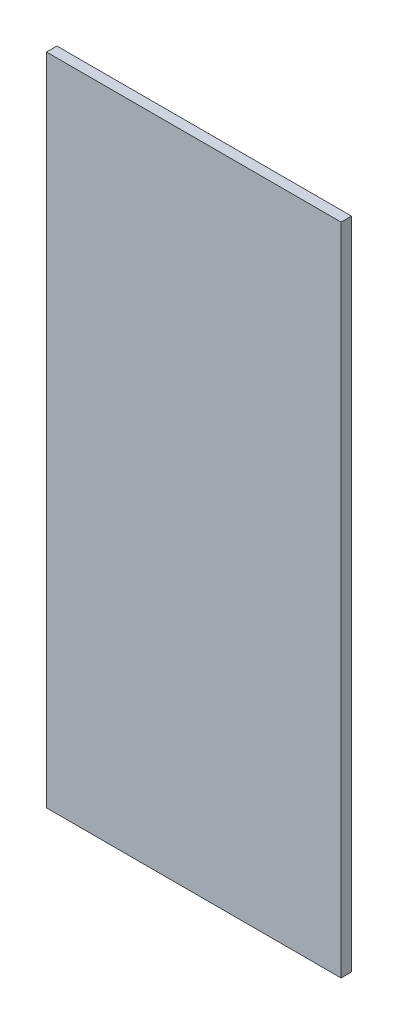
SolidWorks part; units mm, degrees
ref_plane "Front Plane" through (0, 0, 0) normal (0, 0, 1) x (1, 0, 0)
ref_plane "Top Plane" through (0, 0, 0) normal (0, 1, 0) x (1, 0, 0)
ref_plane "Right Plane" through (0, 0, 0) normal (1, 0, 0) x (0, 0, -1)
sketch "Sketch1" plane through (0, 0, 0) normal (0, 0, 1) x (1, 0, 0)
  line L1 (45, -100) -> (-45, -100)
  line L2 (45, -100) -> (45, 100)
  line L3 (45, 100) -> (-45, 100)
  line L4 (-45, -100) -> (-45, 100)
  line L5 (45, -100) -> (-45, 100) construction
  line L6 (45, 100) -> (-45, -100) construction
  point P0 (0, 0)
  dimension "D1" = 90
  dimension "D2" = 200
extrude "Boss-Extrude2" add sketch "Sketch1" along normal blind 3.175
